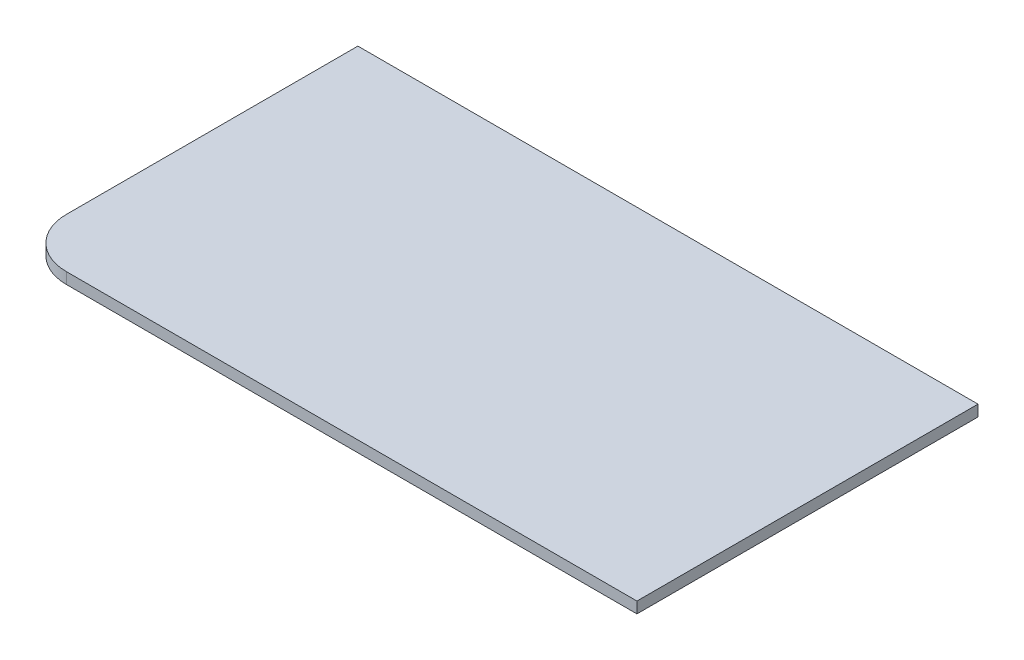
SolidWorks part; units mm, degrees
ref_plane "Front Plane" through (0, 0, 0) normal (0, 0, 1) x (1, 0, 0)
ref_plane "Top Plane" through (0, 0, 0) normal (0, 1, 0) x (1, 0, 0)
ref_plane "Right Plane" through (0, 0, 0) normal (1, 0, 0) x (0, 0, -1)
sketch "Sketch1" plane through (0, 0, 0) normal (0, 1, 0) x (1, 0, 0)
  line L1 (-73.32, 75.2895) -> (926.68, 75.2895)
  line L2 (-73.32, 75.2895) -> (-73.32, -394.7105)
  line L3 (6.68, -474.7105) -> (926.68, -474.7105)
  line L4 (926.68, 75.2895) -> (926.68, -474.7105)
  arc A0 (-73.32, -394.7105) -> (6.68, -474.7105) centre (6.68, -394.7105) ccw
  point P6 (-73.32, -474.7105)
  dimension "D3" = 80
  dimension "D1" = 1000
  dimension "D2" = 550
extrude "Boss-Extrude1" add sketch "Sketch1" along normal blind 18
